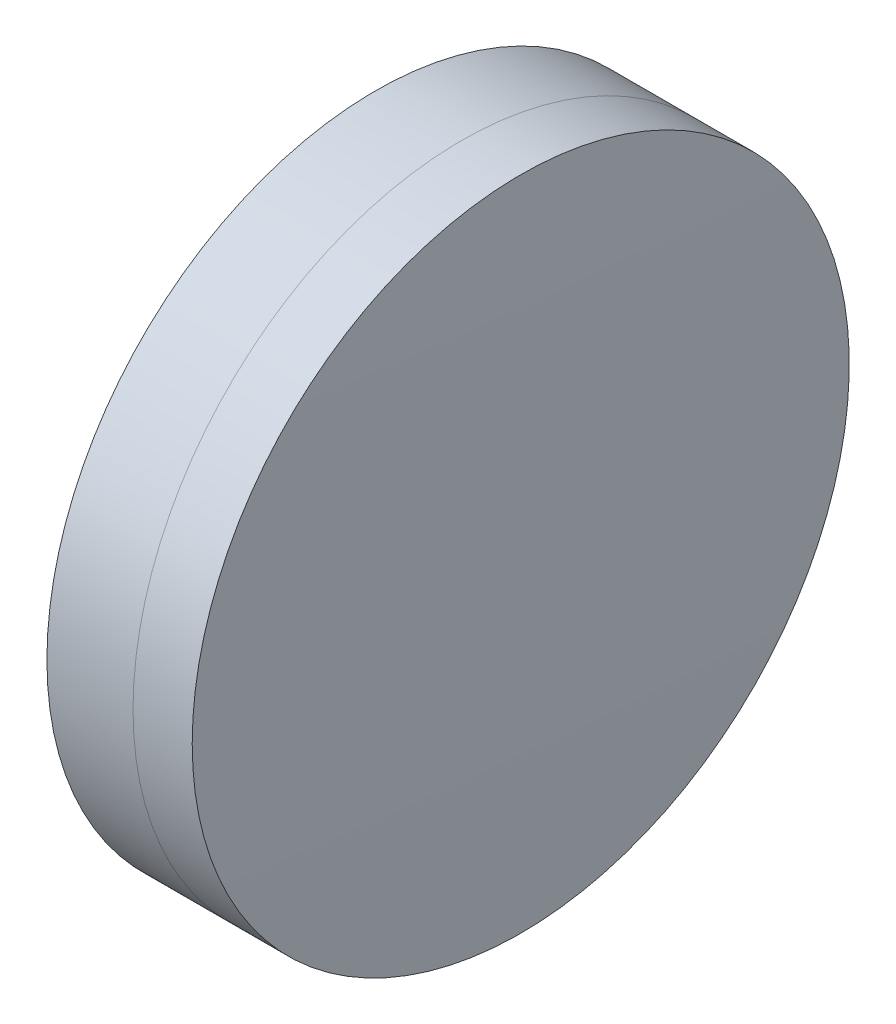
SolidWorks part; units mm, degrees
ref_plane "前视基准面" through (0, 0, 0) normal (0, 0, 1) x (1, 0, 0)
ref_plane "上视基准面" through (0, 0, 0) normal (0, 1, 0) x (1, 0, 0)
ref_plane "右视基准面" through (0, 0, 0) normal (1, 0, 0) x (0, 0, -1)
sketch "草图1" plane through (0, 0, 0) normal (0, 1, 0) x (1, 0, 0)
  line L0 (235.8075, 0) -> (395.1269, 0) construction
  line L1 (363.9386, -12.7) -> (367.2672, -12.7)
  line L2 (363.9386, 12.7) -> (367.2672, 12.7)
  arc A0 (367.2672, -12.7) -> (367.2672, 12.7) centre (180.8994, 0) ccw
  arc A1 (363.9386, 12.7) -> (363.9386, -12.7) centre (700.9994, 0) ccw
  point P10 (363.6994, 0)
  point P11 (367.6994, 0)
  dimension "D3" = 337.3
  dimension "D4" = 186.8
  dimension "D1" = 12.7
  dimension "D2" = 12.7
  dimension "D5" = 4
revolve "旋转1" add sketch "草图1" angle 360 about L0
sketch "草图2" plane through (0, 0, 0) normal (0, 1, 0) x (1, 0, 0)
  line L0 (-0.5519, 0) -> (409.4962, 0) construction
  line L2 (367.2672, 12.7) -> (369.5547, 12.7)
  line L3 (367.2672, -12.7) -> (369.5547, -12.7)
  arc A0 (369.5547, -12.7) -> (369.5547, 12.7) centre (-187.7006, 0) ccw
  arc A1 (367.2672, -12.7) -> (367.2672, 12.7) centre (180.8994, 0) ccw construction
  arc A2 (367.2672, -12.7) -> (367.2672, 12.7) centre (180.8994, 0) ccw
  point P4 (367.6994, 0)
  point P8 (369.6994, 0)
  dimension "D1" = 557.4
  dimension "D2" = 2
revolve "旋转3" add sketch "草图2" angle 360 about L0
